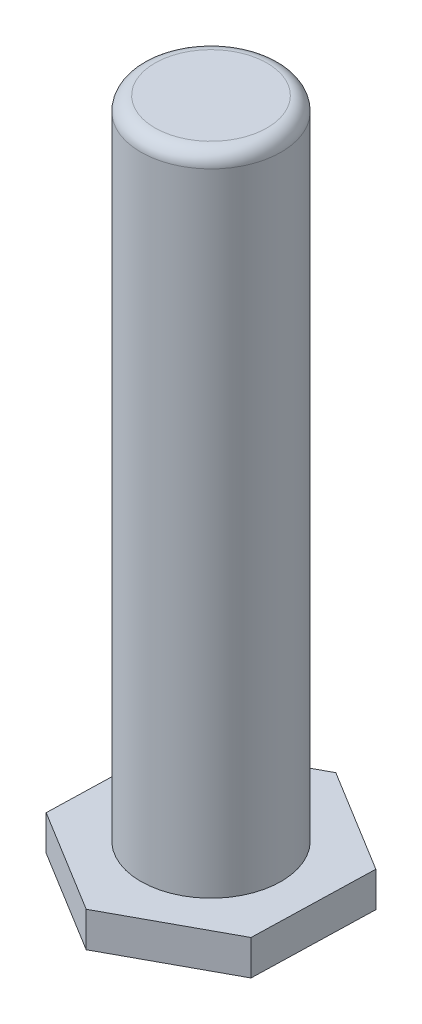
SolidWorks part; units mm, degrees
ref_plane "Plan de face" through (0, 0, 0) normal (0, 0, 1) x (1, 0, 0)
ref_plane "Plan de dessus" through (0, 0, 0) normal (0, 1, 0) x (1, 0, 0)
ref_plane "Plan de droite" through (0, 0, 0) normal (1, 0, 0) x (0, 0, -1)
sketch "Esquisse1" plane through (0, 0, 0) normal (0, 1, 0) x (1, 0, 0)
  line L1 (-14.768, 9.0622) -> (-15.232, -8.2584)
  line L2 (-15.232, -8.2584) -> (-0.4641, -17.3205)
  line L3 (-0.4641, -17.3205) -> (14.768, -9.0622)
  line L4 (14.768, -9.0622) -> (15.232, 8.2584)
  line L5 (15.232, 8.2584) -> (0.4641, 17.3205)
  line L6 (0.4641, 17.3205) -> (-14.768, 9.0622)
  circle A0 centre (0, 0) radius 15.0054 construction
  dimension "D1" = 30
extrude "Boss.-Extru.1" add sketch "Esquisse1" along normal blind 5
sketch "Esquisse2" plane through (0, 5, 0) normal (0, 1, 0) x (1, 0, 0)
  circle A0 centre (0, 0) radius 10
  dimension "D1" = 20
extrude "Boss.-Extru.2" add sketch "Esquisse2" along normal blind 92
cosmetic thread "Représentation de filetage1" parameters "D1"=10, "D2"=14.344
fillet "Congé1" radius 2 1 edges at (0, 97, 10)
